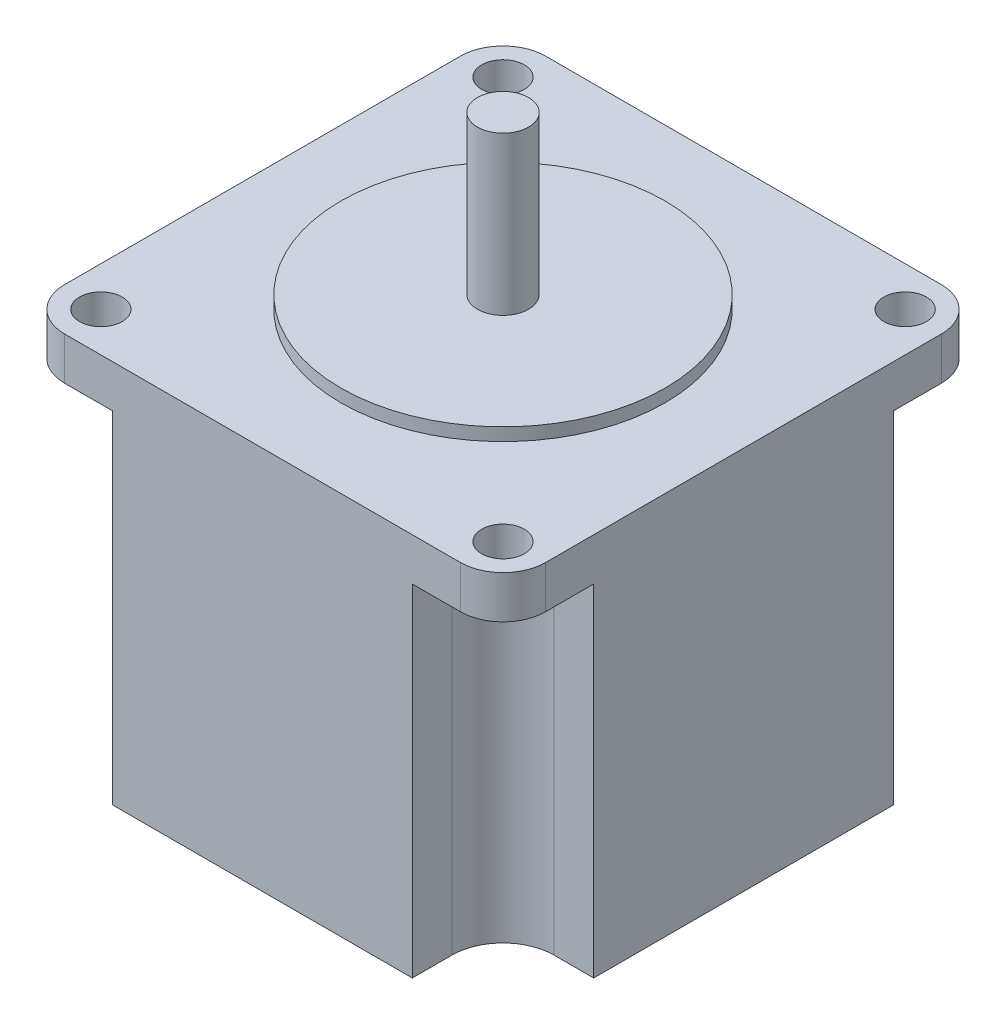
SolidWorks part; units mm, degrees
ref_plane "Front Plane" through (0, 0, 0) normal (0, 0, 1) x (1, 0, 0)
ref_plane "Top Plane" through (0, 0, 0) normal (0, 1, 0) x (1, 0, 0)
ref_plane "Right Plane" through (0, 0, 0) normal (1, 0, 0) x (0, 0, -1)
sketch "Sketch1" plane through (0, 0, 0) normal (0, 1, 0) x (1, 0, 0)
  line L1 (-28.2, -28.2) -> (28.2, -28.2)
  line L2 (-28.2, -28.2) -> (-28.2, 28.2)
  line L3 (-28.2, 28.2) -> (28.2, 28.2)
  line L4 (28.2, -28.2) -> (28.2, 28.2)
  line L5 (-28.2, -28.2) -> (28.2, 28.2) construction
  line L6 (-28.2, 28.2) -> (28.2, -28.2) construction
  circle A0 centre (-23.57, 23.57) radius 2.5
  circle A1 centre (23.57, 23.57) radius 2.5
  circle A2 centre (23.57, -23.57) radius 2.5
  circle A3 centre (-23.57, -23.57) radius 2.5
  point P0 (0, 0)
  dimension "D3" = 5
  dimension "D1" = 47.14
  dimension "D2" = 56.4
sketch "Sketch2" plane through (0, 0, 0) normal (0, 1, 0) x (1, 0, 0)
  line L0 (-28.2, -28.2) -> (-28.2, 28.2) construction
  line L1 (-28.2, 28.2) -> (28.2, 28.2) construction
  line L2 (28.2, -28.2) -> (28.2, 28.2) construction
  line L3 (-28.2, -28.2) -> (28.2, -28.2) construction
  line L4 (-28.2, -23.2) -> (-28.2, 23.2)
  line L5 (-23.2, 28.2) -> (23.2, 28.2)
  line L6 (28.2, -23.2) -> (28.2, 23.2)
  line L7 (-23.2, -28.2) -> (23.2, -28.2)
  arc A0 (-28.2, -23.2) -> (-23.2, -28.2) centre (-23.2, -23.2) ccw
  arc A1 (28.2, -23.2) -> (23.2, -28.2) centre (23.2, -23.2) cw
  arc A2 (23.2, 28.2) -> (28.2, 23.2) centre (23.2, 23.2) cw
  arc A3 (-28.2, 23.2) -> (-23.2, 28.2) centre (-23.2, 23.2) cw
  dimension "D1" = 5
extrude "Boss-Extrude1" add sketch "Sketch2" along normal blind 45
sketch "Sketch3" plane through (0, 0, 0) normal (0, -1, 0) x (1, 0, 0)
  line L0 (-28.2, 17.57) -> (-23.57, 17.57)
  line L1 (-28.2, 28.2) -> (-28.2, -28.2) construction
  line L2 (-17.57, 23.57) -> (-17.57, 28.2)
  line L3 (-28.2, 28.2) -> (28.2, 28.2) construction
  line L4 (-28.2, 28.2) -> (28.2, -28.2) construction
  line L5 (-17.57, 28.2) -> (17.57, 28.2)
  line L6 (0, 28.2) -> (0, 0) construction
  line L7 (-28.2, -28.2) -> (28.2, 28.2) construction
  line L8 (0, 0) -> (-28.2, 0) construction
  line L9 (-28.2, -17.57) -> (-28.2, 17.57)
  line L10 (-17.57, -28.2) -> (17.57, -28.2)
  line L11 (-17.57, -23.57) -> (-17.57, -28.2)
  line L12 (-28.2, -17.57) -> (-23.57, -17.57)
  line L13 (28.2, -17.57) -> (23.57, -17.57)
  line L14 (17.57, -23.57) -> (17.57, -28.2)
  line L15 (28.2, -17.57) -> (28.2, 17.57)
  line L16 (17.57, 23.57) -> (17.57, 28.2)
  line L17 (28.2, 17.57) -> (23.57, 17.57)
  arc A0 (-23.57, 17.57) -> (-17.57, 23.57) centre (-23.57, 23.57) ccw
  arc A1 (-23.57, -17.57) -> (-17.57, -23.57) centre (-23.57, -23.57) cw
  arc A2 (23.57, -17.57) -> (17.57, -23.57) centre (23.57, -23.57) ccw
  arc A3 (23.57, 17.57) -> (17.57, 23.57) centre (23.57, 23.57) cw
  point P31 (0, -28.2)
  dimension "D1" = 6
extrude "Cut-Extrude1" cut sketch "Sketch3" against normal offset from surface (40 mm away) 5 flip side to cut up to face at (0, 45, 0)
sketch "Sketch4" plane through (0, 0, 0) normal (0, 1, 0) x (1, 0, 0)
  circle A0 centre (23.57, -23.57) radius 2.5 construction
  circle A1 centre (-23.57, -23.57) radius 2.5 construction
  circle A2 centre (23.57, 23.57) radius 2.5 construction
  circle A3 centre (-23.57, 23.57) radius 2.5 construction
  circle A4 centre (23.57, -23.57) radius 2.5
  circle A5 centre (-23.57, -23.57) radius 2.5
  circle A6 centre (23.57, 23.57) radius 2.5
  circle A7 centre (-23.57, 23.57) radius 2.5
extrude "Cut-Extrude3" cut sketch "Sketch4" along normal through all both and the other way through all
sketch "Sketch5" plane through (0, 45, 0) normal (0, 1, 0) x (1, 0, 0)
  circle A0 centre (0, 0) radius 19
  dimension "D1" = 38
extrude "Boss-Extrude2" add sketch "Sketch5" along normal blind 1.5
sketch "Sketch6" plane through (0, 46.5, 0) normal (0, 1, 0) x (1, 0, 0)
  line L0 (-28.2, -28.2) -> (28.2, 28.2) construction
  circle A0 centre (0, 0) radius 3
  dimension "D1" = 6
extrude "Boss-Extrude3" add sketch "Sketch6" along normal offset from surface (18.5 mm away) 20 up to face at (0, 45, 19) offset beyond the face yes
